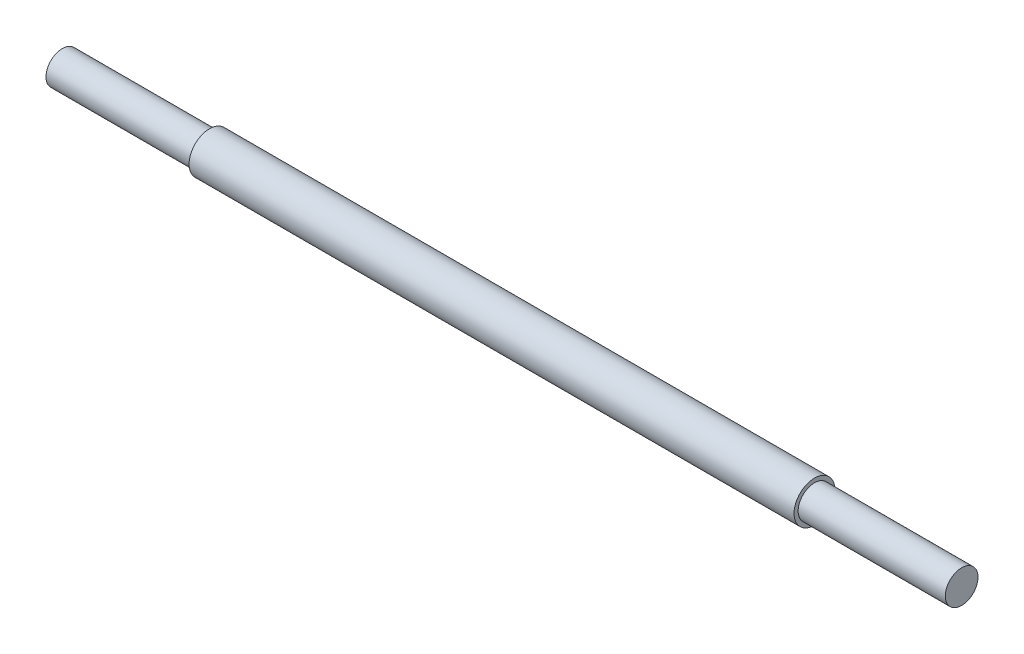
SolidWorks part; units mm, degrees
ref_plane "Front Plane" through (0, 0, 0) normal (0, 0, 1) x (1, 0, 0)
ref_plane "Top Plane" through (0, 0, 0) normal (0, 1, 0) x (1, 0, 0)
ref_plane "Right Plane" through (0, 0, 0) normal (1, 0, 0) x (0, 0, -1)
sketch "Sketch1" plane through (0, 0, 0) normal (1, 0, 0) x (0, 0, -1)
  circle A0 centre (0, 0) radius 2.5
  dimension "D1" = 5
extrude "Boss-Extrude1" add sketch "Sketch1" along normal mid plane 90
sketch "Sketch2" plane through (45, 0, 0) normal (1, 0, 0) x (0, 0, -1)
  circle A0 centre (0, 0) radius 2
  circle A1 centre (0, 0) radius 2.5
  dimension "D1" = 4
extrude "Cut-Extrude1" cut sketch "Sketch2" against normal blind 8
sketch "Sketch3" plane through (-45, 0, 0) normal (-1, 0, 0) x (0, 0, 1)
  circle A0 centre (0, 0) radius 2
  circle A1 centre (0, 0) radius 2.5
  dimension "D1" = 4
extrude "Cut-Extrude2" cut sketch "Sketch3" against normal blind 8
sketch "Sketch4" plane through (45, 0, 0) normal (1, 0, 0) x (0, 0, -1)
  circle A0 centre (0, 0) radius 2
extrude "Boss-Extrude2" add sketch "Sketch4" along normal blind 10
sketch "Sketch5" plane through (-45, 0, 0) normal (-1, 0, 0) x (0, 0, 1)
  circle A0 centre (0, 0) radius 2
extrude "Boss-Extrude3" add sketch "Sketch5" along normal blind 10
